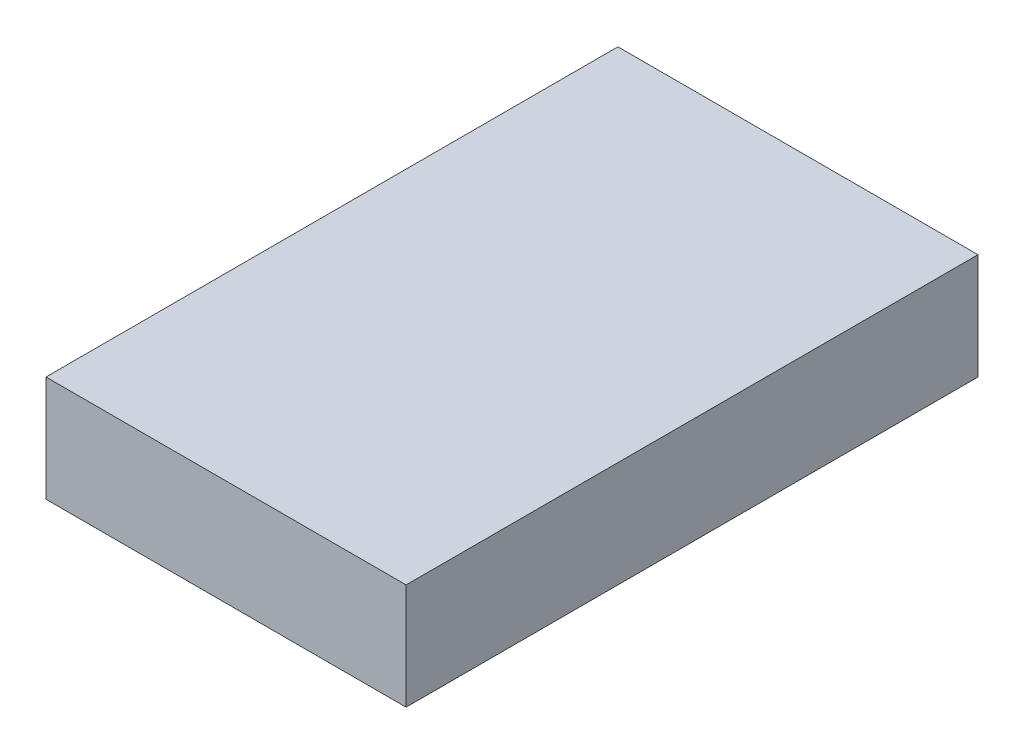
SolidWorks part; units mm, degrees
ref_plane "Front Plane" through (0, 0, 0) normal (0, 0, 1) x (1, 0, 0)
ref_plane "Top Plane" through (0, 0, 0) normal (0, 1, 0) x (1, 0, 0)
ref_plane "Right Plane" through (0, 0, 0) normal (1, 0, 0) x (0, 0, -1)
sketch "BaseS" plane through (0, 0, 0) normal (0, 1, 0) x (1, 0, 0)
  line L1 (-0.68, 1.08) -> (0.68, 1.08)
  line L2 (-0.68, 1.08) -> (-0.68, -1.08)
  line L3 (-0.68, -1.08) -> (0.68, -1.08)
  line L4 (0.68, 1.08) -> (0.68, -1.08)
  line L5 (-0.68, 1.08) -> (0.68, -1.08) construction
  line L6 (-0.68, -1.08) -> (0.68, 1.08) construction
  point P0 (0, 0)
  dimension "Width" = 1.36
  dimension "Length" = 2.16
extrude "Base" add sketch "BaseS" along normal blind 0.4
